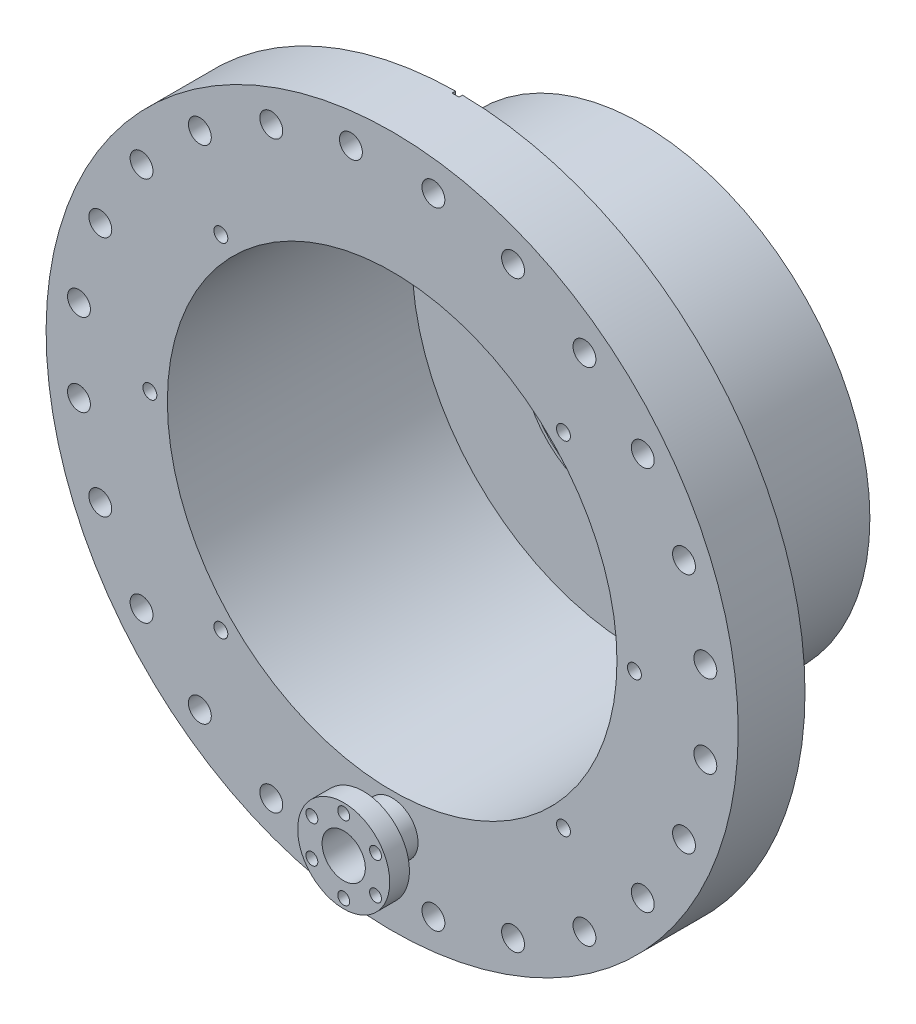
SolidWorks part; units mm, degrees
material "Chrome Stainless Steel"
ref_plane "Front Plane" through (0, 0, 0) normal (0, 0, 1) x (1, 0, 0)
ref_plane "Top Plane" through (0, 0, 0) normal (0, 1, 0) x (1, 0, 0)
ref_plane "Right Plane" through (0, 0, 0) normal (1, 0, 0) x (0, 0, -1)
sketch "Sketch1" plane through (0, 0, 0) normal (0, 0, 1) x (1, 0, 0)
  circle A0 centre (0, 0) radius 83.5
  circle A1 centre (0, 0) radius 82.5
  dimension "D1" = 165
  dimension "D2" = 167
extrude "Extrude1" add sketch "Sketch1" against normal blind 67.31
sketch "Sketch2" plane through (0, 0, 0) normal (0, 0, 1) x (1, 0, 0)
  circle A0 centre (0, 0) radius 82.5
  circle A1 centre (0, 0) radius 127
  circle A2 centre (0, 0) radius 82.5 construction
extrude "Extrude2" add sketch "Sketch2" along normal blind 24.511
sketch "Sketch3" plane through (0, 0, 24.511) normal (0, 0, 1) x (1, 0, 0)
  circle A0 centre (15.1313, -114.9338) radius 4.2
extrude "Cut-Extrude1" cut sketch "Sketch3" against normal up to next (24.511 mm away)
pattern_circular "CirPattern1" count 24 over 360 about axis through (0, 0, 0) along (0, 0, 1) of "Cut-Extrude1"
sketch "Sketch4" plane through (0, 0, -67.31) normal (0, 0, -1) x (-1, 0, 0)
  circle A0 centre (0, 0) radius 83.5
  circle A1 centre (0, 0) radius 32.2
  circle A2 centre (0, 0) radius 83.5 construction
  dimension "D1" = 64.4
extrude "Extrude3" add sketch "Sketch4" against normal blind 2
sketch "Sketch5" plane through (0, 0, 0) normal (0, 1, 0) x (1, 0, 0)
  line L0 (0, 0) -> (0, 106.5628) construction
  line L1 (-32.2, 67.31) -> (-32.2, 55.31)
  line L3 (32.2, 67.31) -> (-32.2, 67.31) construction
  line L4 (83.5, 67.31) -> (-83.5, 67.31) construction
  line L5 (-32.2, 55.31) -> (-31, 55.31)
  line L6 (-31, 55.31) -> (-31, 61.31)
  line L7 (-31, 61.31) -> (-25, 67.31)
  line L8 (-25, 67.31) -> (-32.2, 67.31)
  dimension "D1" = 50
  dimension "D2" = 6
  dimension "D3" = 6
  dimension "D4" = 64.4
  dimension "D5" = 45
revolve "Revolve1" add sketch "Sketch5" angle 360 about L0
sketch "Sketch8" plane through (0, 0, 24.511) normal (0, 0, 1) x (1, 0, 0)
  line L0 (-55, -55) -> (0, 0)
  line L1 (0, 0) -> (-141.2596, 0)
  point P0 (-55, -55)
  dimension "D1" = 45
  dimension "D2" = 55
hole_wizard "#4-40 Tapped Hole1" [suppressed] positions "3DSketch1" profile "Sketch9" tap size "#4-40" standard "Ansi Inch"
sketch3d "3DSketch1"
  point P0 (-55, -55, 24.511)
sketch "Sketch9" plane through (-55, -55, 24.511) normal (1, 0, 0) x (0, -1, 0)
  line L0 (0, 0) -> (0, 8.2992)
  line L1 (0, 8.2992) -> (1.1303, 7.62)
  line L2 (1.1303, 7.62) -> (1.1303, 0)
  line L5 (1.1303, 0) -> (0, 0)
  line L10 (0, 8.2992) -> (-1.1303, 7.62) construction
  line L11 (0, -6.35) -> (0, 107.95) construction
  dimension "Tap Drill Dia." = 2.2606
  dimension "Tap Drill Depth" = 7.62
  dimension "Drill Angle" = 118
cosmetic thread "Hole Thread1" [suppressed] parameters "D1"=5.588, "D2"=2.8448
mirror "Mirror1" [suppressed] about plane through (0, 0, 0) normal (0, 1, 0)
mirror "Mirror2" [suppressed] about plane through (0, 0, 0) normal (1, 0, 0)
sketch "Sketch11" plane through (0, 0, 0) normal (0, 1, 0) x (1, 0, 0)
  line L0 (-31.7, 67.31) -> (-31.7, 61.3171)
  line L1 (-25, 67.31) -> (-32.2, 67.31) construction
  line L2 (-31.7, 61.3171) -> (-25.7071, 67.31)
  line L3 (-25.7071, 67.31) -> (-31.7, 67.31)
  line L4 (-31, 61.31) -> (-25, 67.31) construction
  line L5 (-32.2, 67.31) -> (-32.2, 55.31) construction
  dimension "D1" = 0.5
  dimension "D2" = 0.5
revolve "Cut-Revolve1" cut sketch "Sketch11" angle 360 about L0
sketch "RF Feedtrhough angle and distance sketch" plane through (0, 0, 24.511) normal (0, 0, 1) x (1, 0, 0)
  line L0 (0, 0) -> (0, 136.8547) construction
  line L1 (0, 0) -> (0, -153.071) construction
  circle A0 centre (0, 0) radius 94.25 construction
  point P3 (0, -94.25)
  dimension "D2" = 188.5
  dimension "D1" = 180
ref_plane "Rf Feedthrough flange plane" through (0, 0, 42.291) normal (0, 0, 1) x (1, 0, 0)
sketch "Sketch13" plane through (0, 0, 42.291) normal (0, 0, 1) x (1, 0, 0)
  circle A0 centre (0, -94.25) radius 7.9375
  dimension "D1" = 15.875
extrude "Extrude4" cut sketch "Sketch13" against normal through all
sketch "Sketch14" plane through (0, 0, 42.291) normal (0, 0, 1) x (1, 0, 0)
  circle A0 centre (0, -94.25) radius 7.9375
  circle A1 centre (0, -94.25) radius 9.4996
  dimension "D1" = 18.9992
extrude "Extrude5" add sketch "Sketch14" against normal up to surface (17.78 mm away) up to face at (7.9375, -94.25, 24.511)
sketch "Sketch15" plane through (0, 0, 42.291) normal (0, 0, 1) x (1, 0, 0)
  circle A0 centre (0, -94.25) radius 7.9375
  circle A1 centre (0, -94.25) radius 16.891
  dimension "D1" = 33.782
extrude "Extrude6" add sketch "Sketch15" against normal blind 7.239
sketch "Sketch16" plane through (0, 0, 42.291) normal (0, 0, 1) x (1, 0, 0)
  line L0 (0, 0) -> (0, -94.25) construction
  circle A0 centre (0, -80.7626) radius 2.1844
  dimension "D1" = 4.3688
  dimension "D2" = 13.4874
extrude "Extrude7" cut sketch "Sketch16" against normal blind 7.239
pattern_circular "CirPattern2" count 6 over 360 about axis through (0, -94.25, 0) along (0, 0, 1) of "Extrude7"
sketch "Sketch17" plane through (0, 0, -67.31) normal (0, 0, -1) x (-1, 0, 0)
  line L0 (0, -40.1853) -> (0, 59.5552) construction
  line L1 (-61.4294, -24.0115) -> (-54.5706, -24.0115)
  line L2 (-61.4294, -24.0115) -> (-61.4294, -27.9885)
  line L3 (-61.4294, -27.9885) -> (-54.5706, -27.9885)
  line L4 (-54.5706, -24.0115) -> (-54.5706, -27.9885)
  line L5 (0, 0) -> (-65.9154, 0) construction
  line L6 (-58, -27.9885) -> (-58, -24.0115) construction
  line L7 (-61.4294, -26) -> (-54.5706, -26) construction
  dimension "D1" = 58
  dimension "D2" = 26
extrude "Extrude8" add sketch "Sketch17" along normal blind 7.62
mirror "Mirror3" about plane through (0, 0, 0) normal (0, 1, 0) of "Extrude8"
mirror "Mirror4" about plane through (0, 0, 0) normal (1, 0, 0) of "Extrude8", "Mirror3"
sketch "Sketch18" plane through (0, 0, 24.511) normal (0, 0, 1) x (1, 0, 0)
  line L0 (0, 0) -> (92.2033, 0) construction
  line L1 (0, 0) -> (0, -117.955) construction
  line L2 (63.3193, -63.3193) -> (0, 0) construction
  circle A0 centre (0, 0) radius 88.9 construction
  point P6 (88.9, 0)
  point P7 (62.8618, -62.8618)
  point P8 (62.8618, 62.8618)
  point P11 (-88.9, 0)
  point P12 (-62.8618, 62.8618)
  point P13 (-62.8618, -62.8618)
  dimension "D2" = 177.8
  dimension "D1" = 45
hole_wizard "1/4-20 Tapped Hole1" positions "3DSketch3" profile "Sketch20" tap size "1/4-20" standard "Ansi Inch"
sketch3d "3DSketch3"
  point P0 (62.8618, -62.8618, 24.511)
  point P3 (-62.8618, -62.8618, 24.511)
  point P6 (-88.9, 0, 24.511)
  point P9 (-62.8618, 62.8618, 24.511)
  point P12 (62.8618, 62.8618, 24.511)
  point P15 (88.9, 0, 24.511)
sketch "Sketch20" plane through (62.8618, -62.8618, 24.511) normal (1, 0, 0) x (0, -1, 0)
  line L0 (0, 0) -> (0, 14.2338)
  line L1 (0, 14.2338) -> (2.5527, 12.7)
  line L2 (2.5527, 12.7) -> (2.5527, 0)
  line L5 (2.5527, 0) -> (0, 0)
  line L10 (0, 14.2338) -> (-2.5527, 12.7) construction
  line L11 (0, -6.35) -> (0, 107.95) construction
  dimension "Tap Drill Dia." = 5.1054
  dimension "Tap Drill Depth" = 12.7
  dimension "Drill Angle" = 118
cosmetic thread "Hole Thread2" parameters "D1"=12.7, "D2"=6.35
cosmetic thread "Hole Thread3" parameters "D1"=12.7, "D2"=6.35
cosmetic thread "Hole Thread4" parameters "D1"=12.7, "D2"=6.35
cosmetic thread "Hole Thread5" parameters "D1"=12.7, "D2"=6.35
cosmetic thread "Hole Thread6" parameters "D1"=12.7, "D2"=6.35
cosmetic thread "Hole Thread7" parameters "D1"=12.7, "D2"=6.35
sketch "Sketch21" plane through (0, 0, 0) normal (0, 0, -1) x (-1, 0, 0)
  line L0 (0, 0) -> (-151.7789, 0) construction
  line L1 (0, 0) -> (0, -14.4551) construction
  line L2 (1.27, -132.9872) -> (-1.27, -132.9872)
  line L3 (-1.27, -132.9872) -> (-1.27, -105.5225)
  line L4 (-1.27, -105.5225) -> (1.27, -105.5225)
  line L5 (1.27, -132.9872) -> (1.27, -105.5225)
  line L6 (1.27, 132.9872) -> (1.27, 105.5225)
  line L7 (-1.27, 105.5225) -> (1.27, 105.5225)
  line L8 (-1.27, 132.9872) -> (-1.27, 105.5225)
  line L9 (1.27, 132.9872) -> (-1.27, 132.9872)
  point P10 (0, 105.5225)
  point P11 (0, -132.9872)
  point P12 (0, -105.5225)
  point P13 (0, 132.9872)
  dimension "D1" = 2.54
extrude "Extrude9" cut sketch "Sketch21" against normal blind 1.27
